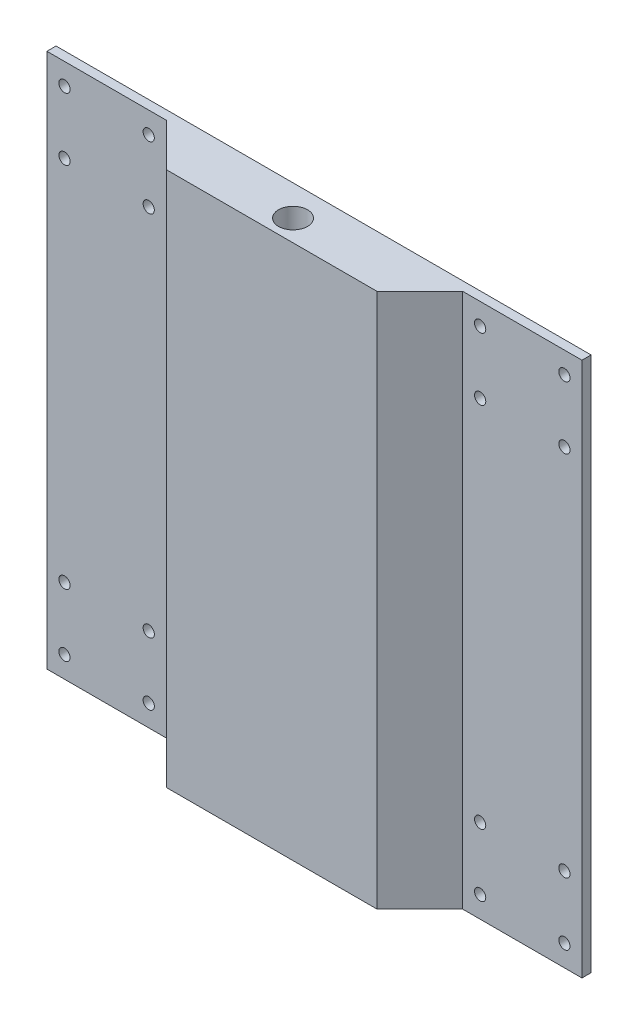
SolidWorks part; units mm, degrees
ref_plane "Front Plane" through (0, 0, 0) normal (0, 0, 1) x (1, 0, 0)
ref_plane "Top Plane" through (0, 0, 0) normal (0, 1, 0) x (1, 0, 0)
ref_plane "Right Plane" through (0, 0, 0) normal (1, 0, 0) x (0, 0, -1)
sketch "Sketch1" plane through (0, 0, 0) normal (0, 0, 1) x (1, 0, 0)
  line L1 (0, 0) -> (152.4, 0)
  line L2 (0, 0) -> (0, 152.4)
  line L3 (0, 152.4) -> (152.4, 152.4)
  line L4 (152.4, 0) -> (152.4, 152.4)
  dimension "D1" = 152.4
  dimension "D2" = 152.4
extrude "Boss-Extrude1" add sketch "Sketch1" along normal blind 2.6
sketch "Sketch2" plane through (0, 0, 2.6) normal (0, 0, 1) x (1, 0, 0)
  line L0 (17, 152.4) -> (17, 122.4) construction
  line L5 (152.4, 0) -> (118.4, 0)
  line L18 (17, 0) -> (135.4, 0)
  line L19 (152.4, 0) -> (152.4, 30)
  line L20 (152.4, 30) -> (118.4, 30)
  line L21 (0, 0) -> (152.4, 0) construction
  line L22 (118.4, 0) -> (118.4, 30)
  line L23 (0, 0) -> (34, 0)
  line L24 (0, 0) -> (0, 30)
  line L25 (0, 30) -> (34, 30)
  line L26 (34, 0) -> (34, 30)
  line L27 (0, 152.4) -> (34, 152.4)
  line L28 (0, 152.4) -> (0, 122.4)
  line L29 (0, 122.4) -> (34, 122.4)
  line L30 (34, 152.4) -> (34, 122.4)
  line L31 (152.4, 152.4) -> (118.4, 152.4)
  line L32 (152.4, 152.4) -> (152.4, 122.4)
  line L33 (152.4, 122.4) -> (118.4, 122.4)
  line L34 (118.4, 152.4) -> (118.4, 122.4)
  line L37 (34, 0) -> (118.4, 0)
  line L39 (0, 137.4) -> (34, 137.4) construction
  line L40 (76.2, 152.4) -> (76.2, 0) construction
  line L41 (152.4, 152.4) -> (0, 152.4) construction
  line L42 (0, 76.2) -> (152.4, 76.2) construction
  line L43 (0, 152.4) -> (0, 0) construction
  line L44 (152.4, 0) -> (152.4, 152.4) construction
  circle A0 centre (5, 146.3) radius 1.6
  circle A1 centre (5, 128.5) radius 1.6
  circle A2 centre (29, 128.5) radius 1.6
  circle A3 centre (29, 146.3) radius 1.6
  circle A4 centre (123.4, 128.5) radius 1.6
  circle A5 centre (147.4, 128.5) radius 1.6
  circle A6 centre (123.4, 146.3) radius 1.6
  circle A7 centre (147.4, 146.3) radius 1.6
  circle A8 centre (147.4, 23.9) radius 1.6
  circle A9 centre (147.4, 6.1) radius 1.6
  circle A10 centre (123.4, 6.1) radius 1.6
  circle A11 centre (123.4, 23.9) radius 1.6
  circle A12 centre (5, 23.9) radius 1.6
  circle A13 centre (29, 23.9) radius 1.6
  circle A14 centre (29, 6.1) radius 1.6
  circle A15 centre (5, 6.1) radius 1.6
  point P6 (76.2, 0)
  dimension "D11" = 3.2
  dimension "D1" = 118.4
  dimension "D2" = 17
  dimension "D3" = 17
  dimension "D4" = 17
  dimension "D5" = 30
  dimension "D6" = 30
  dimension "D7" = 34
  dimension "D8" = 30
  dimension "D9" = 30
  dimension "D10" = 34
  dimension "D12" = 5
  dimension "D13" = 6.1
sketch "Sketch3" plane through (0, 152.4, 0) normal (0, 1, 0) x (1, 0, 0)
  point P2 (76.0556, -9.8654)
sketch "Sketch8" plane through (0, 152.4, 0) normal (0, 1, 0) x (1, 0, 0)
  line L0 (34, -2.6) -> (46.2, -14.8)
  line L1 (34, -2.6) -> (118.4, -2.6)
  line L2 (34, -2.6) -> (118.4, -2.6) construction
  line L6 (46.2, -14.8) -> (106.2, -14.8)
  line L7 (106.2, -14.8) -> (118.4, -2.6)
  line L9 (152.4, -2.6) -> (118.4, -2.6) construction
  line L10 (0, -2.6) -> (0, 0) construction
  line L11 (152.4, 0) -> (0, 0) construction
  point P4 (76.2, -2.6)
  point P5 (112.3, -8.7)
  point P6 (40.1, -8.7)
  point P24 (76.2, -14.8)
  dimension "D1" = 60
  dimension "D2" = 45
extrude "Boss-Extrude4" add sketch "Sketch8" against normal through all
sketch "Sketch9" plane through (0, 152.4, 0) normal (0, 1, 0) x (1, 0, 0)
  line L0 (152.4, 0) -> (0, 0) construction
  line L1 (106.2, -14.8) -> (118.4, -2.6) construction
  circle A0 centre (76.2, -8.7) radius 4
  point P2 (0, 0)
  point P6 (76.2, 0)
  point P9 (112.3, -8.7)
  dimension "D1" = 8
hole_wizard "Tap Drill for M8 Helicoil2" positions "Sketch10" profile "Sketch11" hole size "M8x1.0" standard "ANSI Metric" end condition through all
sketch "Sketch10" plane through (0, 152.4, 0) normal (0, 1, 0) x (1, 0, 0)
  point P0 (76.2, -8.7)
sketch "Sketch11" plane through (76.2, 152.4, 8.7) normal (1, 0, 0) x (0, 0, 1)
  line L0 (0, 0) -> (0, 152.4)
  line L1 (0, 152.4) -> (4.125, 152.4)
  line L2 (4.125, 152.4) -> (4.125, 0)
  line L5 (4.125, 0) -> (0, 0)
  line L11 (0, -6.35) -> (0, 107.95) construction
  dimension "Thru Hole Dia." = 8.25
  dimension "Thru Hole Depth" = 152.4
extrude "Cut-Extrude1" cut sketch "Sketch2" against normal through all contours A1 | A3 | A0 | A2 | A6 | A7 | A5 | A4 | A11 | A8 | A9 | A10 | A12 | A13 | A14 | A15
